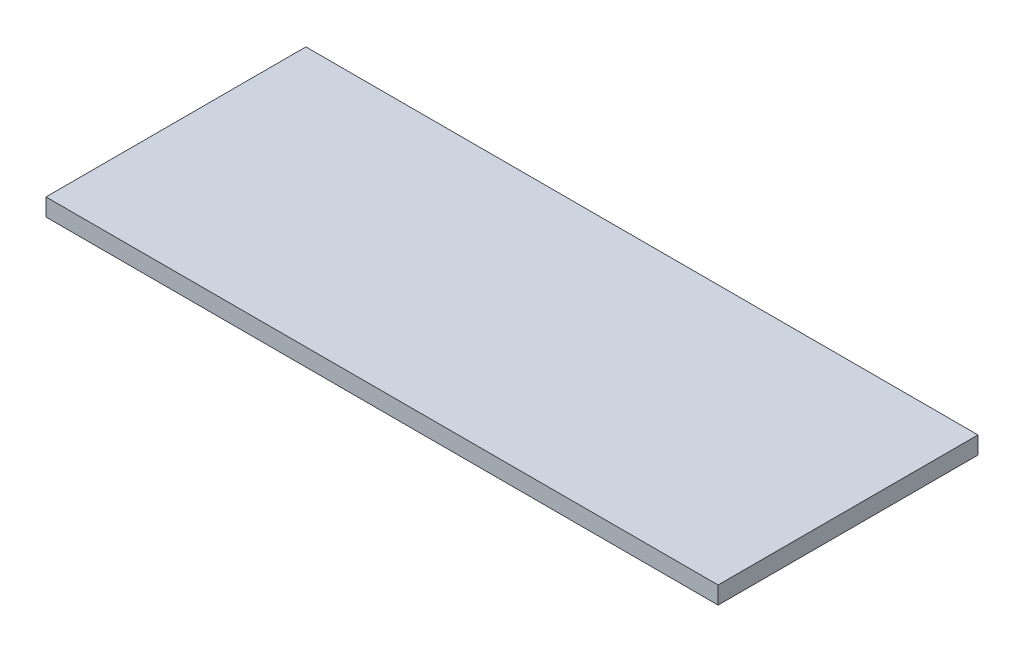
SolidWorks part; units mm, degrees
material "6061-T6 (SS)"
ref_plane "Front Plane" through (0, 0, 0) normal (0, 0, 1) x (1, 0, 0)
ref_plane "Top Plane" through (0, 0, 0) normal (0, 1, 0) x (1, 0, 0)
ref_plane "Right Plane" through (0, 0, 0) normal (1, 0, 0) x (0, 0, -1)
sketch "Sketch1" plane through (0, 0, 0) normal (0, 1, 0) x (1, 0, 0)
  line L1 (66.205, 25.6) -> (-66.205, 25.6)
  line L2 (66.205, 25.6) -> (66.205, -25.6)
  line L3 (66.205, -25.6) -> (-66.205, -25.6)
  line L4 (-66.205, 25.6) -> (-66.205, -25.6)
  line L5 (66.205, 25.6) -> (-66.205, -25.6) construction
  line L6 (66.205, -25.6) -> (-66.205, 25.6) construction
  point P0 (0, 0)
  dimension "D1" = 51.2
  dimension "D2" = 132.41
extrude "Boss-Extrude1" add sketch "Sketch1" along normal blind 3.44
